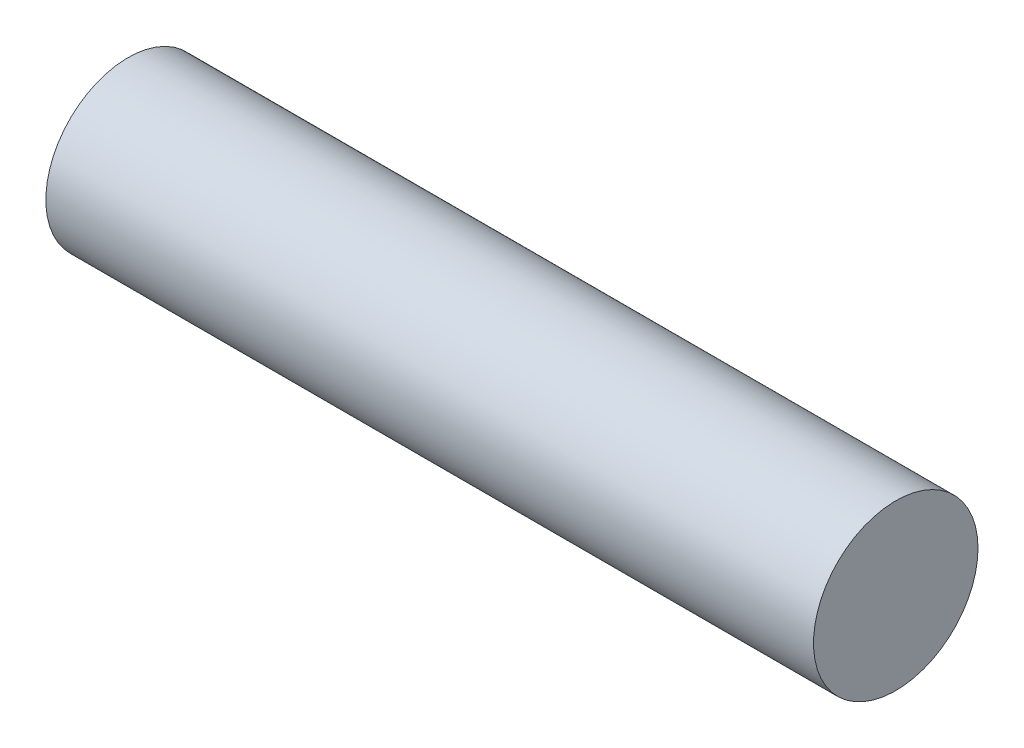
SolidWorks part; units mm, degrees
ref_plane "Front Plane" through (0, 0, 0) normal (0, 0, 1) x (1, 0, 0)
ref_plane "Top Plane" through (0, 0, 0) normal (0, 1, 0) x (1, 0, 0)
ref_plane "Right Plane" through (0, 0, 0) normal (1, 0, 0) x (0, 0, -1)
sketch "Sketch1" plane through (0, 0, 0) normal (1, 0, 0) x (0, 0, -1)
  circle A0 centre (0, 0) radius 2.25
  dimension "D1" = 4.5
extrude "Boss-Extrude1" add sketch "Sketch1" along normal blind 21
